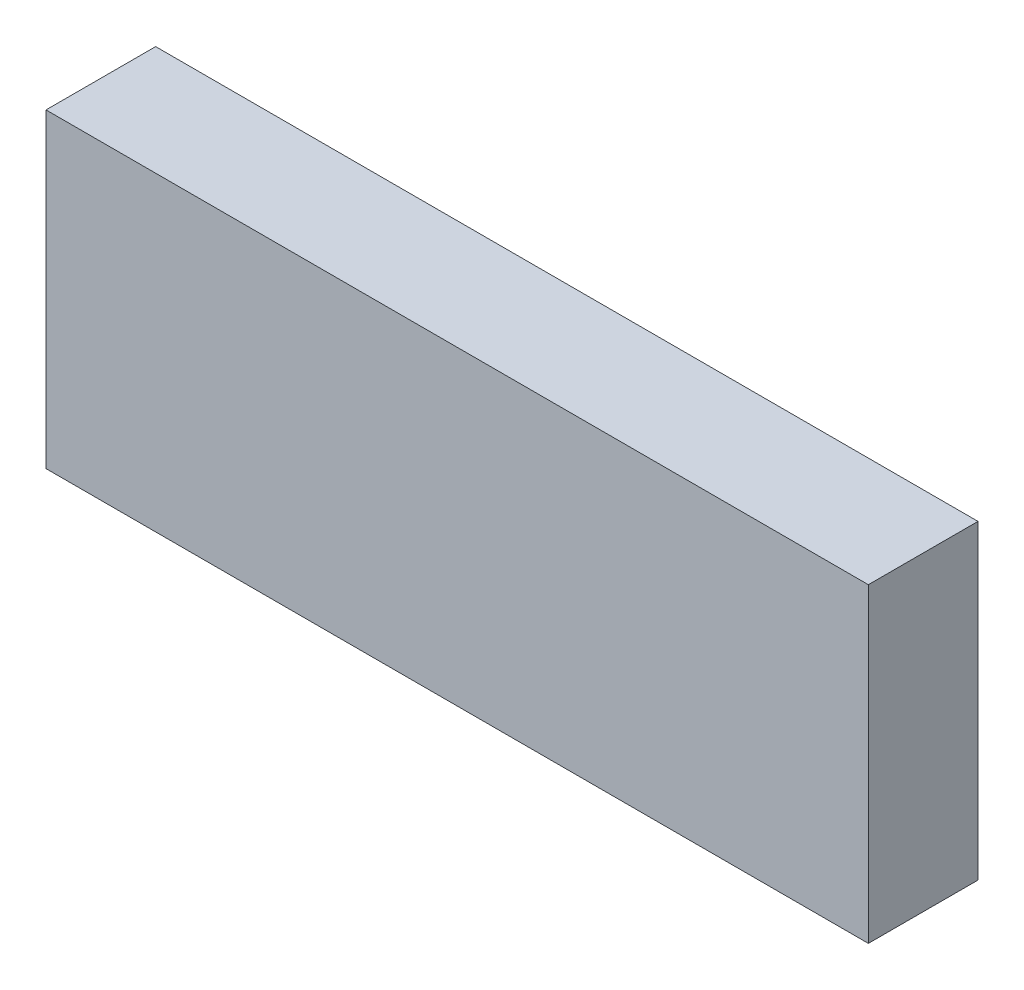
SolidWorks part; units mm, degrees
ref_plane "Ön Düzlem" through (0, 0, 0) normal (0, 0, 1) x (1, 0, 0)
ref_plane "Üst Düzlem" through (0, 0, 0) normal (0, 1, 0) x (1, 0, 0)
ref_plane "Sağ Düzlem" through (0, 0, 0) normal (1, 0, 0) x (0, 0, -1)
sketch "Sketch1" plane through (0, 0, 0) normal (0, 0, 1) x (1, 0, 0)
  line L1 (-23.4866, 17.9258) -> (21.5134, 17.9258)
  line L2 (-23.4866, 17.9258) -> (-23.4866, 0.9258)
  line L3 (-23.4866, 0.9258) -> (21.5134, 0.9258)
  line L4 (21.5134, 17.9258) -> (21.5134, 0.9258)
  dimension "D1" = 45
  dimension "D2" = 17
extrude "Boss-Extrude1" add sketch "Sketch1" along normal blind 6
